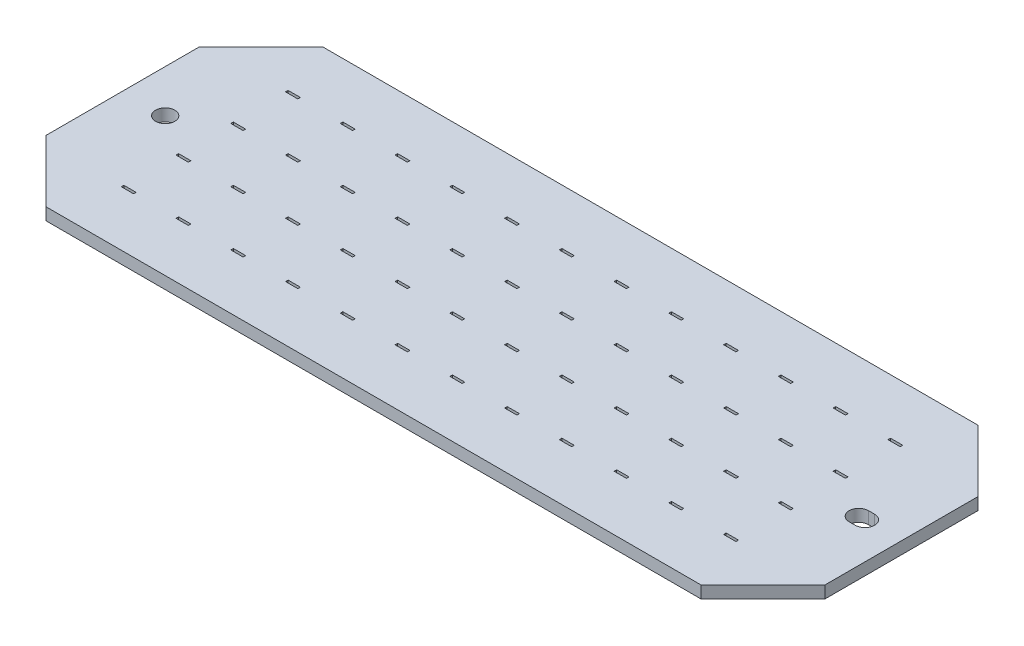
SolidWorks part; units mm, degrees
ref_plane "Front Plane" through (0, 0, 0) normal (0, 0, 1) x (1, 0, 0)
ref_plane "Top Plane" through (0, 0, 0) normal (0, 1, 0) x (1, 0, 0)
ref_plane "Right Plane" through (0, 0, 0) normal (1, 0, 0) x (0, 0, -1)
sketch "Sketch1" plane through (0, 0, 0) normal (0, 1, 0) x (1, 0, 0)
  line L1 (-32, -11.375) -> (32, -11.375)
  line L2 (-32, -11.375) -> (-32, 11.375)
  line L3 (-32, 11.375) -> (32, 11.375)
  line L4 (32, -11.375) -> (32, 11.375)
  line L5 (-32, -11.375) -> (32, 11.375) construction
  line L6 (-32, 11.375) -> (32, -11.375) construction
  point P0 (0, 0)
  dimension "D1" = 22.75
  dimension "D2" = 64
extrude "Extrude1" add sketch "Sketch1" against normal blind 1
chamfer "Chamfer1" distance 5.08 angle 45 4 edges at (-32, -0.5, -11.375) (-32, -0.5, 11.375) (32, -0.5, -11.375) (32, -0.5, 11.375)
sketch "Sketch4" plane through (0, 0, 0) normal (0, 1, 0) x (1, 0, 0)
  line L0 (29, 0.7937) -> (28.5, 0.7937)
  line L1 (28.5, -0.7937) -> (29, -0.7937)
  circle A0 centre (-28.5, 0) radius 0.7937
  arc A1 (28.5, 0.7937) -> (28.5, -0.7937) centre (28.5, 0) ccw
  arc A2 (29, -0.7937) -> (29, 0.7937) centre (29, 0) ccw
extrude "Extrude2" cut sketch "Sketch4" against normal through all
sketch "Sketch5" plane through (0, 0, 0) normal (0, 1, 0) x (-1, 0, 0)
  line L0 (20.755, -6.855) -> (19.745, -6.855)
  line L1 (25.255, -6.855) -> (24.245, -6.855)
  line L2 (25.255, -6.855) -> (25.255, -6.645)
  line L3 (25.255, -6.645) -> (24.245, -6.645)
  line L4 (24.245, -6.855) -> (24.245, -6.645)
  line L5 (25.255, -6.855) -> (24.245, -6.645) construction
  line L6 (25.255, -6.645) -> (24.245, -6.855) construction
  line L7 (20.755, -6.855) -> (20.755, -6.645)
  line L8 (20.755, -6.645) -> (19.745, -6.645)
  line L9 (19.745, -6.855) -> (19.745, -6.645)
  line L10 (20.755, -6.855) -> (19.745, -6.645) construction
  line L11 (20.755, -6.645) -> (19.745, -6.855) construction
  line L12 (16.255, -6.855) -> (15.245, -6.855)
  line L13 (16.255, -6.855) -> (16.255, -6.645)
  line L14 (16.255, -6.645) -> (15.245, -6.645)
  line L15 (15.245, -6.855) -> (15.245, -6.645)
  line L16 (16.255, -6.855) -> (15.245, -6.645) construction
  line L17 (16.255, -6.645) -> (15.245, -6.855) construction
  line L18 (11.755, -6.855) -> (10.745, -6.855)
  line L19 (11.755, -6.855) -> (11.755, -6.645)
  line L20 (11.755, -6.645) -> (10.745, -6.645)
  line L21 (10.745, -6.855) -> (10.745, -6.645)
  line L22 (11.755, -6.855) -> (10.745, -6.645) construction
  line L23 (11.755, -6.645) -> (10.745, -6.855) construction
  line L24 (7.255, -6.855) -> (6.245, -6.855)
  line L25 (7.255, -6.855) -> (7.255, -6.645)
  line L26 (7.255, -6.645) -> (6.245, -6.645)
  line L27 (6.245, -6.855) -> (6.245, -6.645)
  line L28 (7.255, -6.855) -> (6.245, -6.645) construction
  line L29 (7.255, -6.645) -> (6.245, -6.855) construction
  line L30 (2.755, -6.855) -> (1.745, -6.855)
  line L31 (2.755, -6.855) -> (2.755, -6.645)
  line L32 (2.755, -6.645) -> (1.745, -6.645)
  line L33 (1.745, -6.855) -> (1.745, -6.645)
  line L34 (2.755, -6.855) -> (1.745, -6.645) construction
  line L35 (2.755, -6.645) -> (1.745, -6.855) construction
  line L36 (-1.745, -6.855) -> (-2.755, -6.855)
  line L37 (-1.745, -6.855) -> (-1.745, -6.645)
  line L38 (-1.745, -6.645) -> (-2.755, -6.645)
  line L39 (-2.755, -6.855) -> (-2.755, -6.645)
  line L40 (-1.745, -6.855) -> (-2.755, -6.645) construction
  line L41 (-1.745, -6.645) -> (-2.755, -6.855) construction
  line L42 (-6.245, -6.855) -> (-7.255, -6.855)
  line L43 (-6.245, -6.855) -> (-6.245, -6.645)
  line L44 (-6.245, -6.645) -> (-7.255, -6.645)
  line L45 (-7.255, -6.855) -> (-7.255, -6.645)
  line L46 (-6.245, -6.855) -> (-7.255, -6.645) construction
  line L47 (-6.245, -6.645) -> (-7.255, -6.855) construction
  line L48 (-10.745, -6.855) -> (-11.755, -6.855)
  line L49 (-10.745, -6.855) -> (-10.745, -6.645)
  line L50 (-10.745, -6.645) -> (-11.755, -6.645)
  line L51 (-11.755, -6.855) -> (-11.755, -6.645)
  line L52 (-10.745, -6.855) -> (-11.755, -6.645) construction
  line L53 (-10.745, -6.645) -> (-11.755, -6.855) construction
  line L54 (-15.245, -6.855) -> (-16.255, -6.855)
  line L55 (-15.245, -6.855) -> (-15.245, -6.645)
  line L56 (-15.245, -6.645) -> (-16.255, -6.645)
  line L57 (-16.255, -6.855) -> (-16.255, -6.645)
  line L58 (-15.245, -6.855) -> (-16.255, -6.645) construction
  line L59 (-15.245, -6.645) -> (-16.255, -6.855) construction
  line L60 (-19.745, -6.855) -> (-20.755, -6.855)
  line L61 (-19.745, -6.855) -> (-19.745, -6.645)
  line L62 (-19.745, -6.645) -> (-20.755, -6.645)
  line L63 (-20.755, -6.855) -> (-20.755, -6.645)
  line L64 (-19.745, -6.855) -> (-20.755, -6.645) construction
  line L65 (-19.745, -6.645) -> (-20.755, -6.855) construction
  line L66 (-24.245, -6.855) -> (-25.255, -6.855)
  line L67 (-24.245, -6.855) -> (-24.245, -6.645)
  line L68 (-24.245, -6.645) -> (-25.255, -6.645)
  line L69 (-25.255, -6.855) -> (-25.255, -6.645)
  line L70 (-24.245, -6.855) -> (-25.255, -6.645) construction
  line L71 (-24.245, -6.645) -> (-25.255, -6.855) construction
  line L72 (25.255, -2.355) -> (24.245, -2.355)
  line L73 (25.255, -2.355) -> (25.255, -2.145)
  line L74 (25.255, -2.145) -> (24.245, -2.145)
  line L75 (24.245, -2.355) -> (24.245, -2.145)
  line L76 (25.255, -2.355) -> (24.245, -2.145) construction
  line L77 (25.255, -2.145) -> (24.245, -2.355) construction
  line L78 (20.755, -2.355) -> (19.745, -2.355)
  line L79 (20.755, -2.355) -> (20.755, -2.145)
  line L80 (20.755, -2.145) -> (19.745, -2.145)
  line L81 (19.745, -2.355) -> (19.745, -2.145)
  line L82 (20.755, -2.355) -> (19.745, -2.145) construction
  line L83 (20.755, -2.145) -> (19.745, -2.355) construction
  line L84 (16.255, -2.355) -> (15.245, -2.355)
  line L85 (16.255, -2.355) -> (16.255, -2.145)
  line L86 (16.255, -2.145) -> (15.245, -2.145)
  line L87 (15.245, -2.355) -> (15.245, -2.145)
  line L88 (16.255, -2.355) -> (15.245, -2.145) construction
  line L89 (16.255, -2.145) -> (15.245, -2.355) construction
  line L90 (11.755, -2.355) -> (10.745, -2.355)
  line L91 (11.755, -2.355) -> (11.755, -2.145)
  line L92 (11.755, -2.145) -> (10.745, -2.145)
  line L93 (10.745, -2.355) -> (10.745, -2.145)
  line L94 (11.755, -2.355) -> (10.745, -2.145) construction
  line L95 (11.755, -2.145) -> (10.745, -2.355) construction
  line L96 (7.255, -2.355) -> (6.245, -2.355)
  line L97 (7.255, -2.355) -> (7.255, -2.145)
  line L98 (7.255, -2.145) -> (6.245, -2.145)
  line L99 (6.245, -2.355) -> (6.245, -2.145)
  line L100 (7.255, -2.355) -> (6.245, -2.145) construction
  line L101 (7.255, -2.145) -> (6.245, -2.355) construction
  line L102 (2.755, -2.355) -> (1.745, -2.355)
  line L103 (2.755, -2.355) -> (2.755, -2.145)
  line L104 (2.755, -2.145) -> (1.745, -2.145)
  line L105 (1.745, -2.355) -> (1.745, -2.145)
  line L106 (2.755, -2.355) -> (1.745, -2.145) construction
  line L107 (2.755, -2.145) -> (1.745, -2.355) construction
  line L108 (-1.745, -2.355) -> (-2.755, -2.355)
  line L109 (-1.745, -2.355) -> (-1.745, -2.145)
  line L110 (-1.745, -2.145) -> (-2.755, -2.145)
  line L111 (-2.755, -2.355) -> (-2.755, -2.145)
  line L112 (-1.745, -2.355) -> (-2.755, -2.145) construction
  line L113 (-1.745, -2.145) -> (-2.755, -2.355) construction
  line L114 (-6.245, -2.355) -> (-7.255, -2.355)
  line L115 (-6.245, -2.355) -> (-6.245, -2.145)
  line L116 (-6.245, -2.145) -> (-7.255, -2.145)
  line L117 (-7.255, -2.355) -> (-7.255, -2.145)
  line L118 (-6.245, -2.355) -> (-7.255, -2.145) construction
  line L119 (-6.245, -2.145) -> (-7.255, -2.355) construction
  line L120 (-10.745, -2.355) -> (-11.755, -2.355)
  line L121 (-10.745, -2.355) -> (-10.745, -2.145)
  line L122 (-10.745, -2.145) -> (-11.755, -2.145)
  line L123 (-11.755, -2.355) -> (-11.755, -2.145)
  line L124 (-10.745, -2.355) -> (-11.755, -2.145) construction
  line L125 (-10.745, -2.145) -> (-11.755, -2.355) construction
  line L126 (-15.245, -2.355) -> (-16.255, -2.355)
  line L127 (-15.245, -2.355) -> (-15.245, -2.145)
  line L128 (-15.245, -2.145) -> (-16.255, -2.145)
  line L129 (-16.255, -2.355) -> (-16.255, -2.145)
  line L130 (-15.245, -2.355) -> (-16.255, -2.145) construction
  line L131 (-15.245, -2.145) -> (-16.255, -2.355) construction
  line L132 (-19.745, -2.355) -> (-20.755, -2.355)
  line L133 (-19.745, -2.355) -> (-19.745, -2.145)
  line L134 (-19.745, -2.145) -> (-20.755, -2.145)
  line L135 (-20.755, -2.355) -> (-20.755, -2.145)
  line L136 (-19.745, -2.355) -> (-20.755, -2.145) construction
  line L137 (-19.745, -2.145) -> (-20.755, -2.355) construction
  line L138 (-24.245, -2.355) -> (-25.255, -2.355)
  line L139 (-24.245, -2.355) -> (-24.245, -2.145)
  line L140 (-24.245, -2.145) -> (-25.255, -2.145)
  line L141 (-25.255, -2.355) -> (-25.255, -2.145)
  line L142 (-24.245, -2.355) -> (-25.255, -2.145) construction
  line L143 (-24.245, -2.145) -> (-25.255, -2.355) construction
  line L144 (25.255, 2.145) -> (24.245, 2.145)
  line L145 (25.255, 2.145) -> (25.255, 2.355)
  line L146 (25.255, 2.355) -> (24.245, 2.355)
  line L147 (24.245, 2.145) -> (24.245, 2.355)
  line L148 (25.255, 2.145) -> (24.245, 2.355) construction
  line L149 (25.255, 2.355) -> (24.245, 2.145) construction
  line L150 (20.755, 2.145) -> (19.745, 2.145)
  line L151 (20.755, 2.145) -> (20.755, 2.355)
  line L152 (20.755, 2.355) -> (19.745, 2.355)
  line L153 (19.745, 2.145) -> (19.745, 2.355)
  line L154 (20.755, 2.145) -> (19.745, 2.355) construction
  line L155 (20.755, 2.355) -> (19.745, 2.145) construction
  line L156 (16.255, 2.145) -> (15.245, 2.145)
  line L157 (16.255, 2.145) -> (16.255, 2.355)
  line L158 (16.255, 2.355) -> (15.245, 2.355)
  line L159 (15.245, 2.145) -> (15.245, 2.355)
  line L160 (16.255, 2.145) -> (15.245, 2.355) construction
  line L161 (16.255, 2.355) -> (15.245, 2.145) construction
  line L162 (11.755, 2.145) -> (10.745, 2.145)
  line L163 (11.755, 2.145) -> (11.755, 2.355)
  line L164 (11.755, 2.355) -> (10.745, 2.355)
  line L165 (10.745, 2.145) -> (10.745, 2.355)
  line L166 (11.755, 2.145) -> (10.745, 2.355) construction
  line L167 (11.755, 2.355) -> (10.745, 2.145) construction
  line L168 (7.255, 2.145) -> (6.245, 2.145)
  line L169 (7.255, 2.145) -> (7.255, 2.355)
  line L170 (7.255, 2.355) -> (6.245, 2.355)
  line L171 (6.245, 2.145) -> (6.245, 2.355)
  line L172 (7.255, 2.145) -> (6.245, 2.355) construction
  line L173 (7.255, 2.355) -> (6.245, 2.145) construction
  line L174 (2.755, 2.145) -> (1.745, 2.145)
  line L175 (2.755, 2.145) -> (2.755, 2.355)
  line L176 (2.755, 2.355) -> (1.745, 2.355)
  line L177 (1.745, 2.145) -> (1.745, 2.355)
  line L178 (2.755, 2.145) -> (1.745, 2.355) construction
  line L179 (2.755, 2.355) -> (1.745, 2.145) construction
  line L180 (-1.745, 2.145) -> (-2.755, 2.145)
  line L181 (-1.745, 2.145) -> (-1.745, 2.355)
  line L182 (-1.745, 2.355) -> (-2.755, 2.355)
  line L183 (-2.755, 2.145) -> (-2.755, 2.355)
  line L184 (-1.745, 2.145) -> (-2.755, 2.355) construction
  line L185 (-1.745, 2.355) -> (-2.755, 2.145) construction
  line L186 (-6.245, 2.145) -> (-7.255, 2.145)
  line L187 (-6.245, 2.145) -> (-6.245, 2.355)
  line L188 (-6.245, 2.355) -> (-7.255, 2.355)
  line L189 (-7.255, 2.145) -> (-7.255, 2.355)
  line L190 (-6.245, 2.145) -> (-7.255, 2.355) construction
  line L191 (-6.245, 2.355) -> (-7.255, 2.145) construction
  line L192 (-10.745, 2.145) -> (-11.755, 2.145)
  line L193 (-10.745, 2.145) -> (-10.745, 2.355)
  line L194 (-10.745, 2.355) -> (-11.755, 2.355)
  line L195 (-11.755, 2.145) -> (-11.755, 2.355)
  line L196 (-10.745, 2.145) -> (-11.755, 2.355) construction
  line L197 (-10.745, 2.355) -> (-11.755, 2.145) construction
  line L198 (-15.245, 2.145) -> (-16.255, 2.145)
  line L199 (-15.245, 2.145) -> (-15.245, 2.355)
  line L200 (-15.245, 2.355) -> (-16.255, 2.355)
  line L201 (-16.255, 2.145) -> (-16.255, 2.355)
  line L202 (-15.245, 2.145) -> (-16.255, 2.355) construction
  line L203 (-15.245, 2.355) -> (-16.255, 2.145) construction
  line L204 (-19.745, 2.145) -> (-20.755, 2.145)
  line L205 (-19.745, 2.145) -> (-19.745, 2.355)
  line L206 (-19.745, 2.355) -> (-20.755, 2.355)
  line L207 (-20.755, 2.145) -> (-20.755, 2.355)
  line L208 (-19.745, 2.145) -> (-20.755, 2.355) construction
  line L209 (-19.745, 2.355) -> (-20.755, 2.145) construction
  line L210 (-24.245, 2.145) -> (-25.255, 2.145)
  line L211 (-24.245, 2.145) -> (-24.245, 2.355)
  line L212 (-24.245, 2.355) -> (-25.255, 2.355)
  line L213 (-25.255, 2.145) -> (-25.255, 2.355)
  line L214 (-24.245, 2.145) -> (-25.255, 2.355) construction
  line L215 (-24.245, 2.355) -> (-25.255, 2.145) construction
  line L216 (25.255, 6.645) -> (24.245, 6.645)
  line L217 (25.255, 6.645) -> (25.255, 6.855)
  line L218 (25.255, 6.855) -> (24.245, 6.855)
  line L219 (24.245, 6.645) -> (24.245, 6.855)
  line L220 (25.255, 6.645) -> (24.245, 6.855) construction
  line L221 (25.255, 6.855) -> (24.245, 6.645) construction
  line L222 (20.755, 6.645) -> (19.745, 6.645)
  line L223 (20.755, 6.645) -> (20.755, 6.855)
  line L224 (20.755, 6.855) -> (19.745, 6.855)
  line L225 (19.745, 6.645) -> (19.745, 6.855)
  line L226 (20.755, 6.645) -> (19.745, 6.855) construction
  line L227 (20.755, 6.855) -> (19.745, 6.645) construction
  line L228 (16.255, 6.645) -> (15.245, 6.645)
  line L229 (16.255, 6.645) -> (16.255, 6.855)
  line L230 (16.255, 6.855) -> (15.245, 6.855)
  line L231 (15.245, 6.645) -> (15.245, 6.855)
  line L232 (16.255, 6.645) -> (15.245, 6.855) construction
  line L233 (16.255, 6.855) -> (15.245, 6.645) construction
  line L234 (11.755, 6.645) -> (10.745, 6.645)
  line L235 (11.755, 6.645) -> (11.755, 6.855)
  line L236 (11.755, 6.855) -> (10.745, 6.855)
  line L237 (10.745, 6.645) -> (10.745, 6.855)
  line L238 (11.755, 6.645) -> (10.745, 6.855) construction
  line L239 (11.755, 6.855) -> (10.745, 6.645) construction
  line L240 (7.255, 6.645) -> (6.245, 6.645)
  line L241 (7.255, 6.645) -> (7.255, 6.855)
  line L242 (7.255, 6.855) -> (6.245, 6.855)
  line L243 (6.245, 6.645) -> (6.245, 6.855)
  line L244 (7.255, 6.645) -> (6.245, 6.855) construction
  line L245 (7.255, 6.855) -> (6.245, 6.645) construction
  line L246 (2.755, 6.645) -> (1.745, 6.645)
  line L247 (2.755, 6.645) -> (2.755, 6.855)
  line L248 (2.755, 6.855) -> (1.745, 6.855)
  line L249 (1.745, 6.645) -> (1.745, 6.855)
  line L250 (2.755, 6.645) -> (1.745, 6.855) construction
  line L251 (2.755, 6.855) -> (1.745, 6.645) construction
  line L252 (-1.745, 6.645) -> (-2.755, 6.645)
  line L253 (-1.745, 6.645) -> (-1.745, 6.855)
  line L254 (-1.745, 6.855) -> (-2.755, 6.855)
  line L255 (-2.755, 6.645) -> (-2.755, 6.855)
  line L256 (-1.745, 6.645) -> (-2.755, 6.855) construction
  line L257 (-1.745, 6.855) -> (-2.755, 6.645) construction
  line L258 (-6.245, 6.645) -> (-7.255, 6.645)
  line L259 (-6.245, 6.645) -> (-6.245, 6.855)
  line L260 (-6.245, 6.855) -> (-7.255, 6.855)
  line L261 (-7.255, 6.645) -> (-7.255, 6.855)
  line L262 (-6.245, 6.645) -> (-7.255, 6.855) construction
  line L263 (-6.245, 6.855) -> (-7.255, 6.645) construction
  line L264 (-10.745, 6.645) -> (-11.755, 6.645)
  line L265 (-10.745, 6.645) -> (-10.745, 6.855)
  line L266 (-10.745, 6.855) -> (-11.755, 6.855)
  line L267 (-11.755, 6.645) -> (-11.755, 6.855)
  line L268 (-10.745, 6.645) -> (-11.755, 6.855) construction
  line L269 (-10.745, 6.855) -> (-11.755, 6.645) construction
  line L270 (-15.245, 6.645) -> (-16.255, 6.645)
  line L271 (-15.245, 6.645) -> (-15.245, 6.855)
  line L272 (-15.245, 6.855) -> (-16.255, 6.855)
  line L273 (-16.255, 6.645) -> (-16.255, 6.855)
  line L274 (-15.245, 6.645) -> (-16.255, 6.855) construction
  line L275 (-15.245, 6.855) -> (-16.255, 6.645) construction
  line L276 (-19.745, 6.645) -> (-20.755, 6.645)
  line L277 (-19.745, 6.645) -> (-19.745, 6.855)
  line L278 (-19.745, 6.855) -> (-20.755, 6.855)
  line L279 (-20.755, 6.645) -> (-20.755, 6.855)
  line L280 (-19.745, 6.645) -> (-20.755, 6.855) construction
  line L281 (-19.745, 6.855) -> (-20.755, 6.645) construction
  line L282 (-24.245, 6.645) -> (-25.255, 6.645)
  line L283 (-24.245, 6.645) -> (-24.245, 6.855)
  line L284 (-24.245, 6.855) -> (-25.255, 6.855)
  line L285 (-25.255, 6.645) -> (-25.255, 6.855)
  line L286 (-24.245, 6.645) -> (-25.255, 6.855) construction
  line L287 (-24.245, 6.855) -> (-25.255, 6.645) construction
  point P0 (24.75, -6.75)
  point P8 (20.25, -6.75)
  point P13 (15.75, -6.75)
  point P18 (11.25, -6.75)
  point P23 (6.75, -6.75)
  point P28 (2.25, -6.75)
  point P33 (-2.25, -6.75)
  point P38 (-6.75, -6.75)
  point P43 (-11.25, -6.75)
  point P48 (-15.75, -6.75)
  point P53 (-20.25, -6.75)
  point P58 (-24.75, -6.75)
  point P63 (24.75, -2.25)
  point P68 (20.25, -2.25)
  point P73 (15.75, -2.25)
  point P78 (11.25, -2.25)
  point P83 (6.75, -2.25)
  point P88 (2.25, -2.25)
  point P93 (-2.25, -2.25)
  point P98 (-6.75, -2.25)
  point P103 (-11.25, -2.25)
  point P108 (-15.75, -2.25)
  point P113 (-20.25, -2.25)
  point P118 (-24.75, -2.25)
  point P123 (24.75, 2.25)
  point P128 (20.25, 2.25)
  point P133 (15.75, 2.25)
  point P138 (11.25, 2.25)
  point P143 (6.75, 2.25)
  point P148 (2.25, 2.25)
  point P153 (-2.25, 2.25)
  point P158 (-6.75, 2.25)
  point P163 (-11.25, 2.25)
  point P168 (-15.75, 2.25)
  point P173 (-20.25, 2.25)
  point P178 (-24.75, 2.25)
  point P183 (24.75, 6.75)
  point P188 (20.25, 6.75)
  point P193 (15.75, 6.75)
  point P198 (11.25, 6.75)
  point P203 (6.75, 6.75)
  point P208 (2.25, 6.75)
  point P213 (-2.25, 6.75)
  point P218 (-6.75, 6.75)
  point P223 (-11.25, 6.75)
  point P228 (-15.75, 6.75)
  point P233 (-20.25, 6.75)
  point P238 (-24.75, 6.75)
  dimension "D1" = 0.21
  dimension "D2" = 1.01
extrude "Extrude5" cut sketch "Sketch5" against normal through all draft 4
